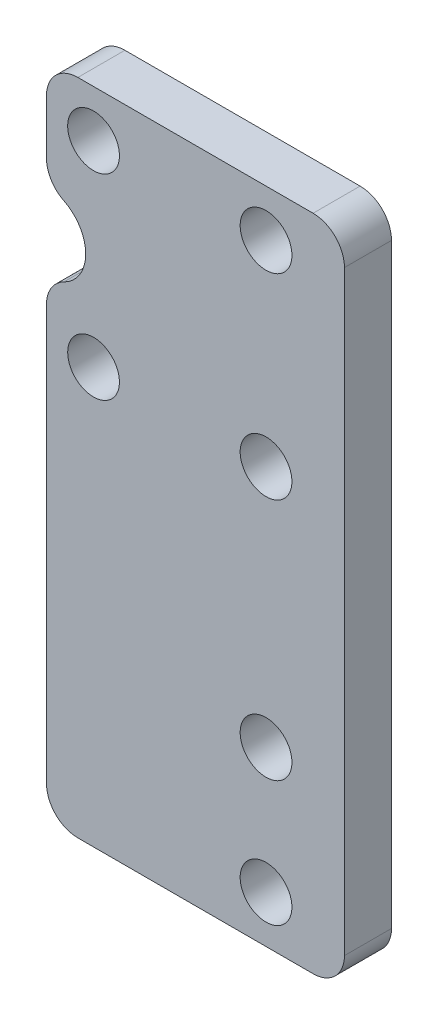
SolidWorks part; units mm, degrees
material "A-玻璃纤维"
ref_plane "前视基准面" through (0, 0, 0) normal (0, 0, 1) x (1, 0, 0)
ref_plane "上视基准面" through (0, 0, 0) normal (0, 1, 0) x (1, 0, 0)
ref_plane "右视基准面" through (0, 0, 0) normal (1, 0, 0) x (0, 0, -1)
sketch "草图1" plane through (0, 0, 0) normal (0, 0, 1) x (1, 0, 0)
  line L6 (-6.5, 21) -> (-6.5, -21) construction
  line L7 (-9.5, 21) -> (9.5, 21)
  line L8 (-9.5, 21) -> (-9.5, -21)
  line L9 (-9.5, -21) -> (9.5, -21)
  line L10 (9.5, 21) -> (9.5, -21)
  line L11 (-9.5, 21) -> (9.5, -21) construction
  line L12 (-9.5, -21) -> (9.5, 21) construction
  line L13 (0, 0) -> (-42.8628, 0) construction
  line L14 (4.5, -10) -> (4.5, -18) construction
  line L15 (1.5, 21) -> (1.5, -21) construction
  line L16 (0, 0) -> (0, -33.8165) construction
  line L17 (-6.5, 18) -> (13.1713, 18) construction
  line L18 (-6.5, 5.5) -> (17.9469, 5.5) construction
  circle A0 centre (-6.5, 18) radius 1.65
  circle A1 centre (-6.5, 5.5) radius 1.65
  circle A2 centre (4.5, -10) radius 1.65
  circle A3 centre (4.5, -18) radius 1.65
  circle A6 centre (4.5, 18) radius 1.65
  circle A7 centre (4.5, 5.5) radius 1.65
  point P0 (0, 0)
  dimension "D1" = 3.3
  dimension "D2" = 12.5
  dimension "D4" = 3.3
  dimension "D5" = 8
  dimension "D9" = 31
  dimension "D10" = 3
  dimension "D11" = 11
  dimension "D3" = 42
  dimension "D6" = 8
  dimension "D7" = 19
  dimension "D8" = 8
  dimension "D12" = 5
extrude "凸台-拉伸1" add sketch "草图1" along normal blind 3
sketch "草图2" plane through (0, 0, 3) normal (0, 0, 1) x (1, 0, 0)
  line L0 (-9.5, 21) -> (-9.5, -21) construction
  line L1 (9.5, 21) -> (-9.5, 21) construction
  circle A0 centre (-9.5, 11.5) radius 2.5
  dimension "D1" = 5
  dimension "D2" = 9.5
extrude "切除-拉伸1" cut sketch "草图2" against normal through all
fillet "圆角1" radius 2 2 edges at (-9.5, 9, 1.5) (-9.5, 14, 1.5)
fillet "圆角2" radius 2 4 edges at (-9.5, 21, 1.5) (9.5, 21, 1.5) (9.5, -21, 1.5) (-9.5, -21, 1.5)
